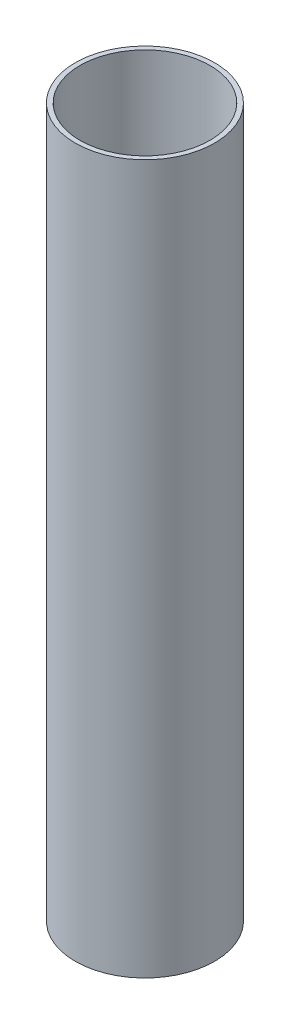
SolidWorks part; units mm, degrees
ref_plane "Front Plane" through (0, 0, 0) normal (0, 0, 1) x (1, 0, 0)
ref_plane "Top Plane" through (0, 0, 0) normal (0, 1, 0) x (1, 0, 0)
ref_plane "Right Plane" through (0, 0, 0) normal (1, 0, 0) x (0, 0, -1)
sketch "Sketch1" plane through (0, 0, 0) normal (0, 1, 0) x (1, 0, 0)
  circle A0 centre (0, 0) radius 29.5
  circle A1 centre (0, 0) radius 27.5
  dimension "D1" = 55
  dimension "D2" = 59
extrude "Boss-Extrude1" add sketch "Sketch1" along normal blind 300
sketch "Sketch2" plane through (0, 300, 0) normal (0, 1, 0) x (1, 0, 0)
  line L0 (-65.3571, 18.4647) -> (-30, 43.0842)
  line L1 (30, 43.0842) -> (65.3571, 18.4647)
  line L2 (65.3571, -18.4647) -> (30, -43.0842)
  line L3 (-65.3571, -18.4647) -> (-30, -43.0842)
  arc A0 (-30, -43.0842) -> (30, -43.0842) centre (0, 0) ccw
  arc A1 (65.3571, -18.4647) -> (65.3571, 18.4647) centre (52.5, 0) ccw
  arc A2 (-65.3571, 18.4647) -> (-65.3571, -18.4647) centre (-52.5, 0) ccw
  arc A3 (30, 43.0842) -> (-30, 43.0842) centre (0, 0) ccw
  circle A4 centre (-52.5, 0) radius 4
  circle A5 centre (52.5, 0) radius 4
  circle A8 centre (0, 0) radius 27.5 construction
  circle A9 centre (0, 0) radius 27.5
  dimension "D1" = 105
  dimension "D2" = 45
  dimension "D3" = 45
  dimension "D4" = 8
  dimension "D5" = 8
extrude "Boss-Extrude2" [suppressed] add sketch "Sketch2" along normal blind 5
sketch "Sketch3" [suppressed] plane through (0, 0, 0) normal (0, 0, 1) x (1, 0, 0)
  line L0 (-194.2145, 195) -> (49805.7855, 195) construction
  line L1 (30, 305) -> (-30, 305) construction
  line L2 (0, 0) -> (0, 50000) construction
  circle A0 centre (0, 195) radius 1.5
  circle A1 centre (0, 185) radius 1.5
  circle A2 centre (0, 175) radius 1.5
  dimension "D4" = 3
  dimension "D5" = 3
  dimension "D6" = 3
  dimension "D1" = 110
  dimension "D2" = 10
  dimension "D3" = 10
extrude "Cut-Extrude1" [suppressed] cut sketch "Sketch3" against normal through all both and the other way through all
sketch "Sketch4" [suppressed] plane through (0, 0, 0) normal (1, 0, 0) x (0, 0, -1)
  line L0 (0, 0) -> (0, 50000) construction
  line L1 (0, 195) -> (-50000, 195) construction
  line L2 (18.4647, 305) -> (-18.4647, 305) construction
  circle A0 centre (0, 185) radius 1.5
  circle A1 centre (0, 195) radius 1.5
  circle A2 centre (0, 175) radius 1.5
  dimension "D2" = 3
  dimension "D1" = 110
  dimension "D3" = 10
  dimension "D4" = 10
extrude "Cut-Extrude2" [suppressed] cut sketch "Sketch4" against normal through all both and the other way through all
ref_plane "Plane1" through (0, 0, 0) normal (-0.7071, 0, 0.7071) x (0, -1, 0)
ref_plane "Plane2" through (0, 0, 0) normal (-0.7071, 0, -0.7071) x (0, -1, 0)
pattern_linear "LPattern1" [suppressed] count 3 spacing 60
sketch "Sketch5" [suppressed] plane through (0, 0, 0) normal (-0.7071, 0, -0.7071) x (0, -1, 0)
  line L0 (-187, 0) -> (-187, 50000) construction
  line L2 (0, 0) -> (-50000, 0) construction
  line L4 (-305, -9.2519) -> (-305, 33.158) construction
  circle A0 centre (-187, 0) radius 1.5
  circle A1 centre (-177, 0) radius 1.5
  circle A2 centre (-167, 0) radius 1.5
  dimension "D4" = 3
  dimension "D1" = 118
  dimension "D2" = 10
  dimension "D3" = 10
extrude "Cut-Extrude3" [suppressed] cut sketch "Sketch5" against normal through all both and the other way through all
sketch "Sketch6" [suppressed] plane through (0, 0, 0) normal (-0.7071, 0, 0.7071) x (0, -1, 0)
  line L0 (-187, 0) -> (-187, 50000) construction
  line L2 (0, 0) -> (-50000, 0) construction
  line L4 (-305, -33.158) -> (-305, 9.2519) construction
  circle A0 centre (-187, 0) radius 1.5
  circle A1 centre (-177, 0) radius 1.5
  circle A2 centre (-167, 0) radius 1.5
  dimension "D2" = 3
  dimension "D1" = 118
  dimension "D3" = 3
extrude "Cut-Extrude4" [suppressed] cut sketch "Sketch6" against normal through all both and the other way through all
pattern_linear "LPattern2" [suppressed] count 3 spacing 65
